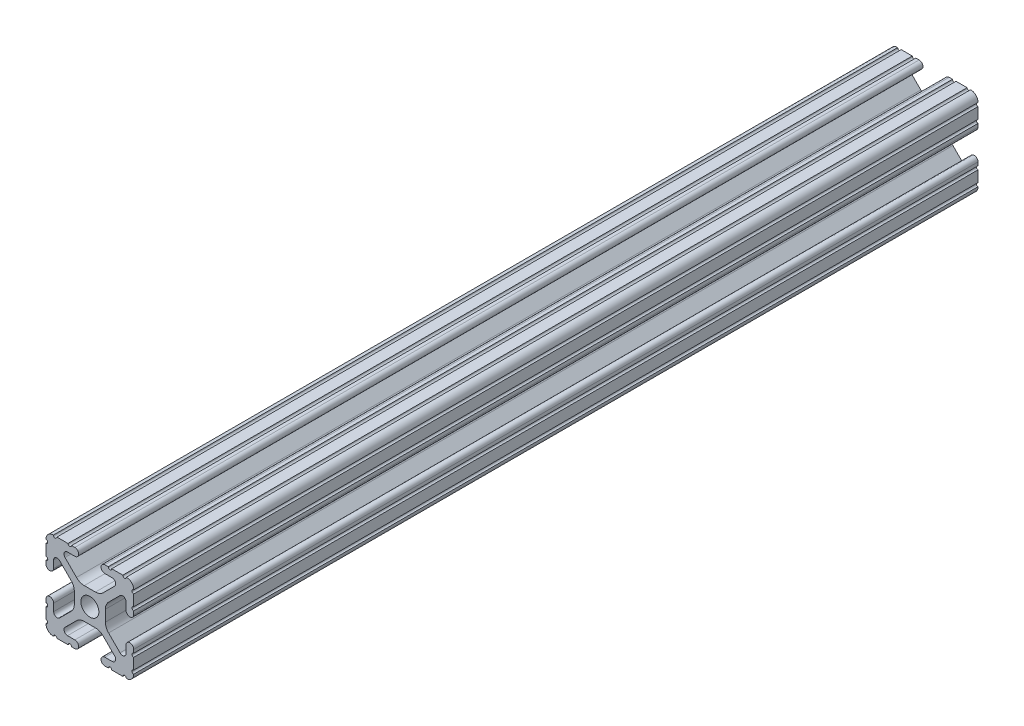
SolidWorks part; units mm, degrees
material "6061-T6 (SS)"
ref_plane "Front Plane" through (0, 0, 0) normal (0, 0, 1) x (1, 0, 0)
ref_plane "Top Plane" through (0, 0, 0) normal (0, 1, 0) x (1, 0, 0)
ref_plane "Right Plane" through (0, 0, 0) normal (1, 0, 0) x (0, 0, -1)
ref_plane "Plane1" through (0, 0, -450.85) normal (0, 0, -1) x (-1, 0, 0)
sketch "Sketch1" plane through (0, 0, -450.85) normal (0, 0, -1) x (-1, 0, 0)
  line L0 (12.7, -9.5504) -> (12.7, -6.3331)
  line L1 (12.7, -5.3171) -> (12.7, -4.3434)
  line L2 (10.4902, -4.3434) -> (10.4902, -6.4748)
  line L3 (8.7558, -7.1932) -> (5.4257, -3.8632)
  line L4 (4.4958, -1.6181) -> (4.4958, 1.6181)
  line L5 (5.4257, 3.8632) -> (8.7558, 7.1932)
  line L6 (10.4902, 6.4748) -> (10.4902, 4.3434)
  line L7 (12.7, 4.3434) -> (12.7, 5.3171)
  line L8 (12.7, 6.3331) -> (12.7, 9.5504)
  line L9 (9.5504, 12.7) -> (6.3331, 12.7)
  line L10 (5.3171, 12.7) -> (4.3434, 12.7)
  line L11 (4.3434, 10.4902) -> (6.4748, 10.4902)
  line L12 (7.1932, 8.7558) -> (3.8632, 5.4257)
  line L13 (1.6181, 4.4958) -> (-1.6181, 4.4958)
  line L14 (-3.8632, 5.4257) -> (-7.1932, 8.7558)
  line L15 (-6.4748, 10.4902) -> (-4.3434, 10.4902)
  line L16 (-4.3434, 12.7) -> (-5.3171, 12.7)
  line L17 (-6.3331, 12.7) -> (-9.5504, 12.7)
  line L18 (-12.7, 9.5504) -> (-12.7, 6.3331)
  line L19 (-12.7, 5.3171) -> (-12.7, 4.3434)
  line L20 (-10.4902, 4.3434) -> (-10.4902, 6.4748)
  line L21 (-8.7558, 7.1932) -> (-5.4257, 3.8632)
  line L22 (-4.4958, 1.6181) -> (-4.4958, -1.6181)
  line L23 (-5.4257, -3.8632) -> (-8.7558, -7.1932)
  line L24 (-10.4902, -6.4748) -> (-10.4902, -4.3434)
  line L25 (-12.7, -4.3434) -> (-12.7, -5.3171)
  line L26 (-12.7, -6.3331) -> (-12.7, -9.5504)
  line L27 (-9.5504, -12.7) -> (-6.3331, -12.7)
  line L28 (-5.3171, -12.7) -> (-4.3434, -12.7)
  line L29 (-4.3434, -10.4902) -> (-6.4748, -10.4902)
  line L30 (-7.1932, -8.7558) -> (-3.8632, -5.4257)
  line L31 (-1.6181, -4.4958) -> (1.6181, -4.4958)
  line L32 (3.8632, -5.4257) -> (7.1932, -8.7558)
  line L33 (6.4748, -10.4902) -> (4.3434, -10.4902)
  line L34 (4.3434, -12.7) -> (5.3171, -12.7)
  line L35 (6.3331, -12.7) -> (9.5504, -12.7)
  arc A0 (12.6998, -10.5664) -> (12.7, -9.5504) centre (12.7, -10.0584) cw
  arc A1 (12.7, -6.3331) -> (12.7, -5.3171) centre (12.7, -5.8251) cw
  arc A2 (12.7, -4.3434) -> (10.4902, -4.3434) centre (11.5951, -4.3434) ccw
  arc A3 (10.4902, -6.4748) -> (8.7558, -7.1932) centre (9.4742, -6.4748) cw
  arc A4 (5.4257, -3.8632) -> (4.4958, -1.6181) centre (7.6708, -1.6181) cw
  arc A5 (4.4958, 1.6181) -> (5.4257, 3.8632) centre (7.6708, 1.6181) cw
  arc A6 (8.7558, 7.1932) -> (10.4902, 6.4748) centre (9.4742, 6.4748) cw
  arc A7 (10.4902, 4.3434) -> (12.7, 4.3434) centre (11.5951, 4.3434) ccw
  arc A8 (12.7, 5.3171) -> (12.7, 6.3331) centre (12.7, 5.8251) cw
  arc A9 (12.7, 9.5504) -> (12.6998, 10.5664) centre (12.7, 10.0584) cw
  arc A10 (12.6998, 10.5664) -> (10.5664, 12.6998) centre (10.5918, 10.5918) ccw
  arc A11 (10.5664, 12.6998) -> (9.5504, 12.7) centre (10.0584, 12.7) cw
  arc A12 (6.3331, 12.7) -> (5.3171, 12.7) centre (5.8251, 12.7) cw
  arc A13 (4.3434, 12.7) -> (4.3434, 10.4902) centre (4.3434, 11.5951) ccw
  arc A14 (6.4748, 10.4902) -> (7.1932, 8.7558) centre (6.4748, 9.4742) cw
  arc A15 (3.8632, 5.4257) -> (1.6181, 4.4958) centre (1.6181, 7.6708) cw
  arc A16 (-1.6181, 4.4958) -> (-3.8632, 5.4257) centre (-1.6181, 7.6708) cw
  arc A17 (-7.1932, 8.7558) -> (-6.4748, 10.4902) centre (-6.4748, 9.4742) cw
  arc A18 (-4.3434, 10.4902) -> (-4.3434, 12.7) centre (-4.3434, 11.5951) ccw
  arc A19 (-5.3171, 12.7) -> (-6.3331, 12.7) centre (-5.8251, 12.7) cw
  arc A20 (-9.5504, 12.7) -> (-10.5664, 12.6998) centre (-10.0584, 12.7) cw
  arc A21 (-10.5664, 12.6998) -> (-12.6998, 10.5664) centre (-10.5918, 10.5918) ccw
  arc A22 (-12.6998, 10.5664) -> (-12.7, 9.5504) centre (-12.7, 10.0584) cw
  arc A23 (-12.7, 6.3331) -> (-12.7, 5.3171) centre (-12.7, 5.8251) cw
  arc A24 (-12.7, 4.3434) -> (-10.4902, 4.3434) centre (-11.5951, 4.3434) ccw
  arc A25 (-10.4902, 6.4748) -> (-8.7558, 7.1932) centre (-9.4742, 6.4748) cw
  arc A26 (-5.4257, 3.8632) -> (-4.4958, 1.6181) centre (-7.6708, 1.6181) cw
  arc A27 (-4.4958, -1.6181) -> (-5.4257, -3.8632) centre (-7.6708, -1.6181) cw
  arc A28 (-8.7558, -7.1932) -> (-10.4902, -6.4748) centre (-9.4742, -6.4748) cw
  arc A29 (-10.4902, -4.3434) -> (-12.7, -4.3434) centre (-11.5951, -4.3434) ccw
  arc A30 (-12.7, -5.3171) -> (-12.7, -6.3331) centre (-12.7, -5.8251) cw
  arc A31 (-12.7, -9.5504) -> (-12.6998, -10.5664) centre (-12.7, -10.0584) cw
  arc A32 (-12.6998, -10.5664) -> (-10.5664, -12.6998) centre (-10.5918, -10.5918) ccw
  arc A33 (-10.5664, -12.6998) -> (-9.5504, -12.7) centre (-10.0584, -12.7) cw
  arc A34 (-6.3331, -12.7) -> (-5.3171, -12.7) centre (-5.8251, -12.7) cw
  arc A35 (-4.3434, -12.7) -> (-4.3434, -10.4902) centre (-4.3434, -11.5951) ccw
  arc A36 (-6.4748, -10.4902) -> (-7.1932, -8.7558) centre (-6.4748, -9.4742) cw
  arc A37 (-3.8632, -5.4257) -> (-1.6181, -4.4958) centre (-1.6181, -7.6708) cw
  arc A38 (1.6181, -4.4958) -> (3.8632, -5.4257) centre (1.6181, -7.6708) cw
  arc A39 (7.1932, -8.7558) -> (6.4748, -10.4902) centre (6.4748, -9.4742) cw
  arc A40 (4.3434, -10.4902) -> (4.3434, -12.7) centre (4.3434, -11.5951) ccw
  arc A41 (5.3171, -12.7) -> (6.3331, -12.7) centre (5.8251, -12.7) cw
  arc A42 (9.5504, -12.7) -> (10.5664, -12.6998) centre (10.0584, -12.7) cw
  arc A43 (10.5664, -12.6998) -> (12.6998, -10.5664) centre (10.5918, -10.5918) ccw
  circle A44 centre (0, 0) radius 2.6035
extrude "Boss-Extrude1" add sketch "Sketch1" against normal mid plane 244.5512
